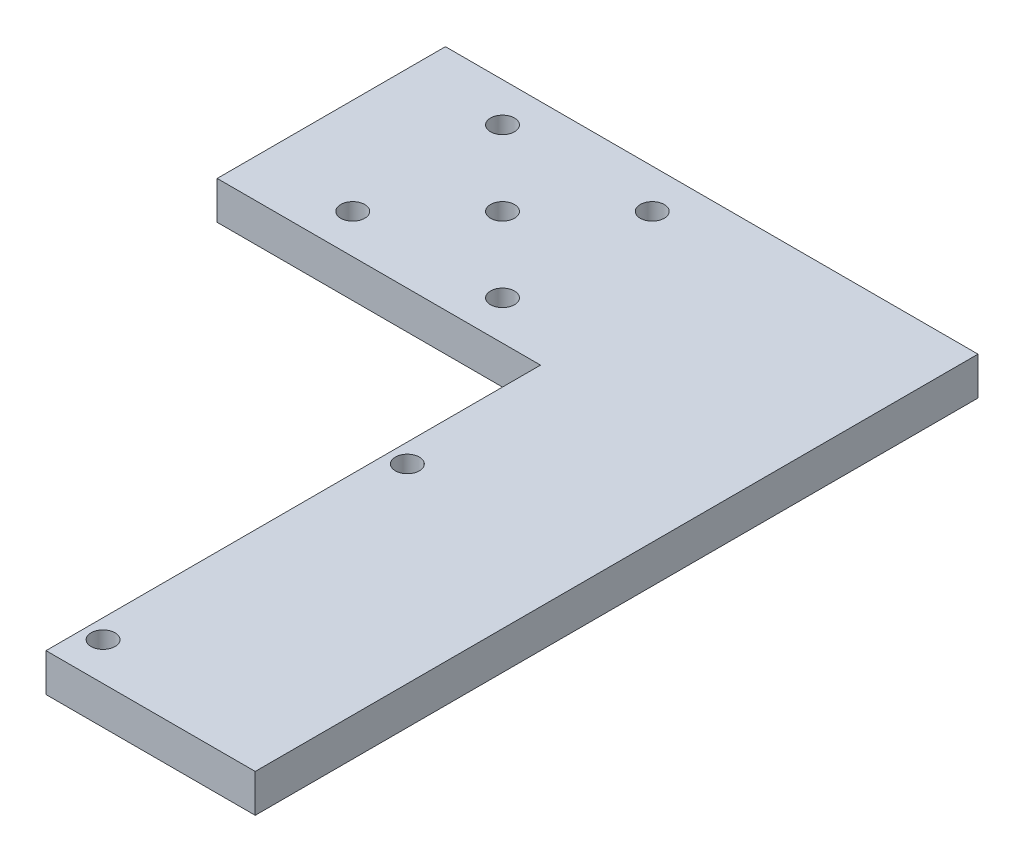
SolidWorks part; units mm, degrees
ref_plane "Front Plane" through (0, 0, 0) normal (0, 0, 1) x (1, 0, 0)
ref_plane "Top Plane" through (0, 0, 0) normal (0, 1, 0) x (1, 0, 0)
ref_plane "Right Plane" through (0, 0, 0) normal (1, 0, 0) x (0, 0, -1)
sketch "Sketch1" plane through (0, 0, 0) normal (0, 1, 0) x (1, 0, 0)
  line L0 (53.975, 38.1) -> (53.975, 0) construction
  line L2 (0, 0) -> (0, 38.1)
  line L4 (88.9, 0) -> (88.9, 38.1)
  line L5 (16.075, 31.55) -> (16.075, 6.55) construction
  line L6 (16.075, 6.55) -> (41.075, 6.55) construction
  line L7 (0, 38.1) -> (53.975, 38.1) construction
  line L9 (0, 38.1) -> (88.9, 38.1)
  line L10 (0, 0) -> (53.975, 0)
  line L11 (53.975, 0) -> (88.9, 0) construction
  line L12 (53.975, 0) -> (53.975, -82.55)
  line L13 (53.975, -82.55) -> (88.9, -82.55)
  line L14 (88.9, -82.55) -> (88.9, 0)
  line L15 (0, 38.1) -> (53.975, 38.1)
  circle A4 centre (16.075, 31.55) radius 2
  circle A5 centre (41.075, 31.55) radius 2
  circle A7 centre (16.075, 6.55) radius 2
  circle A8 centre (41.075, 6.55) radius 2
  circle A9 centre (28.575, 19.05) radius 2
  circle A10 centre (57.15, -25.4) radius 2
  circle A11 centre (57.15, -76.2) radius 2
  point P16 (16.075, 19.05)
  point P17 (53.975, 19.05)
  point P20 (28.575, 6.55)
  point P26 (0, 0)
  point P27 (0, 0)
  dimension "D3" = 4
  dimension "D7" = 4
  dimension "D1" = 38.1
  dimension "D2" = 88.9
  dimension "D4" = 25
  dimension "D5" = 25
  dimension "D6" = 28.575
  dimension "D8" = 3.175
  dimension "D9" = 50.8
  dimension "D10" = 6.35
  dimension "D11" = 82.55
  dimension "D12" = 53.975
extrude "Boss-Extrude1" add sketch "Sketch1" along normal blind 6.35
